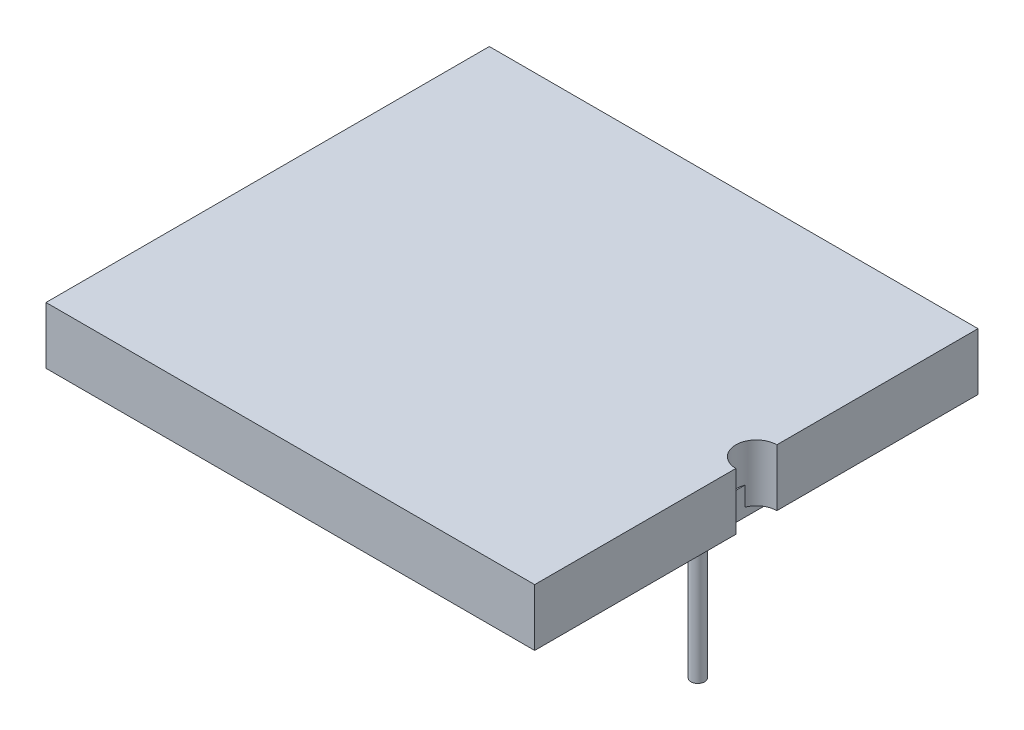
SolidWorks part; units mm, degrees
ref_plane "Front Plane" through (0, 0, 0) normal (0, 0, 1) x (1, 0, 0)
ref_plane "Top Plane" through (0, 0, 0) normal (0, 1, 0) x (1, 0, 0)
ref_plane "Right Plane" through (0, 0, 0) normal (1, 0, 0) x (0, 0, -1)
sketch "Sketch1" plane through (0, 0, 0) normal (0, 1, 0) x (1, 0, 0)
  line L0 (8.35, -0.7) -> (8.35, -7.575)
  line L1 (8.35, 7.575) -> (-8.35, 7.575)
  line L2 (8.35, 7.575) -> (8.35, 0.7)
  line L3 (8.35, -7.575) -> (-8.35, -7.575)
  line L4 (-8.35, 7.575) -> (-8.35, -7.575)
  line L5 (8.35, 7.575) -> (-8.35, -7.575) construction
  line L6 (8.35, -7.575) -> (-8.35, 7.575) construction
  arc A0 (8.35, 0.7) -> (8.35, -0.7) centre (8.35, 0) ccw
  point P0 (0, 0)
  dimension "D3" = 0.7
  dimension "D1" = 16.7
  dimension "D2" = 15.15
extrude "Boss-Extrude1" add sketch "Sketch1" against normal blind 1.95
sketch "Sketch3" plane through (0, -1.95, 0) normal (0, -1, 0) x (1, 0, 0)
  line L1 (5, 5) -> (-5, 5)
  line L2 (5, 5) -> (5, -5)
  line L3 (5, -5) -> (-5, -5)
  line L4 (-5, 5) -> (-5, -5)
  line L5 (5, 5) -> (-5, -5) construction
  line L6 (5, -5) -> (-5, 5) construction
  point P0 (0, 0)
  dimension "D1" = 10
  dimension "D2" = 10
extrude "Boss-Extrude6" add sketch "Sketch3" against normal blind 1.05 from surface at 0 separate body starting at face at (2.6667, -1.95, 0)
sketch "Sketch12" plane through (0, -1.95, 0) normal (0, -1, 0) x (1, 0, 0)
  line L1 (7.7, -7) -> (-7.7, -7)
  line L2 (7.7, -7) -> (7.7, 7)
  line L3 (7.7, 7) -> (-7.7, 7)
  line L4 (-7.7, -7) -> (-7.7, 7)
  line L5 (7.7, -7) -> (-7.7, 7) construction
  line L6 (7.7, 7) -> (-7.7, -7) construction
  point P0 (0, 0)
  dimension "D1" = 15.4
  dimension "D2" = 14
extrude "Boss-Extrude11" add sketch "Sketch12" along normal blind 0.3 and the other way offset from surface (0.65 mm away) 0.4 separate body other way up to face at (0, -0.9, 0)
sketch "Sketch13" plane through (0, -2.25, 0) normal (0, -1, 0) x (1, 0, 0)
  line L0 (8.35, -7.575) -> (-8.35, -7.575) construction
  line L1 (0, -1.0545) -> (0, 1.766) construction
  circle A0 centre (-6.35, 0) radius 0.5
  circle A1 centre (6.35, 0) radius 0.5
  dimension "D1" = 1
  dimension "D2" = 7.575
  dimension "D3" = 6.35
extrude "Boss-Extrude12" add sketch "Sketch13" along normal blind 0.3 draft 41
sketch "Sketch14" plane through (0, -2.55, 0) normal (0, -1, 0) x (1, 0, 0)
  line L0 (0, -0.5491) -> (0, 1.1461) construction
  circle A0 centre (-6.35, 0) radius 0.2329
  circle A1 centre (6.35, 0) radius 0.2329
  dimension "D1" = 0.4658
extrude "Boss-Extrude15" add sketch "Sketch14" along normal blind 5 and the other way up to surface (1.25 mm away) separate body other way up to face at (0, -1.3, 0)
